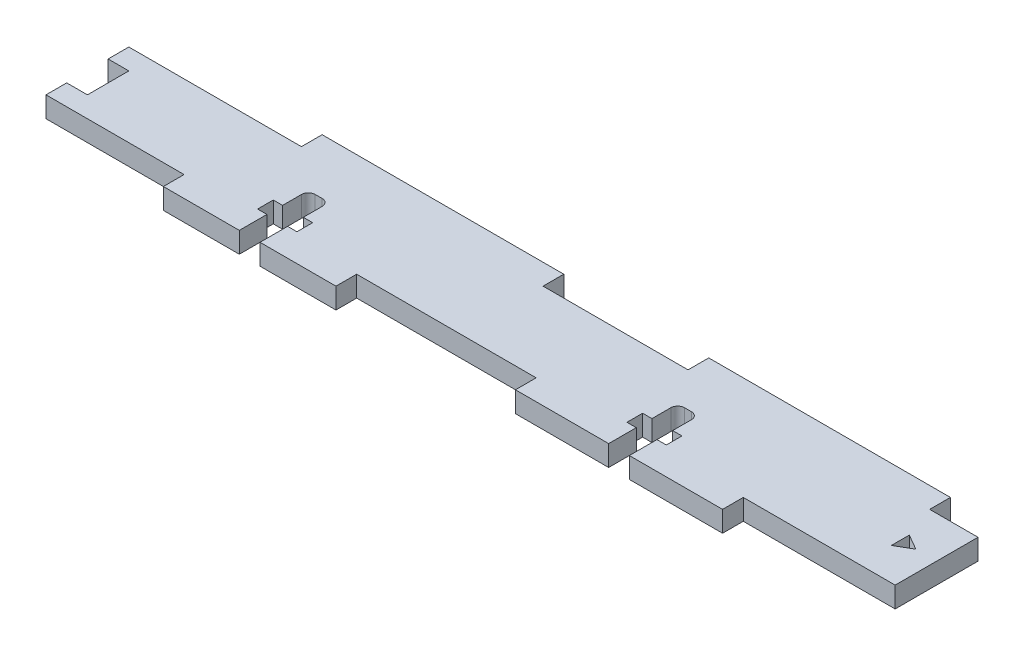
SolidWorks part; units mm, degrees
material "Acrylic (Medium-high impact)"
ref_plane "Plano frontal" through (0, 0, 0) normal (0, 0, 1) x (1, 0, 0)
ref_plane "Plano superior" through (0, 0, 0) normal (0, 1, 0) x (1, 0, 0)
ref_plane "Plano direito" through (0, 0, 0) normal (1, 0, 0) x (0, 0, -1)
sketch "Sketch1" plane through (0, 0, 0) normal (0, 1, 0) x (1, 0, 0)
  line L1 (-61.5, 6) -> (61.5, 6)
  line L2 (-61.5, 6) -> (-61.5, -6)
  line L3 (-61.5, -6) -> (61.5, -6)
  line L4 (61.5, 6) -> (61.5, -6)
  point P4 (0, 6)
  point P6 (-61.5, 0)
  dimension "D1" = 123
  dimension "D2" = 12
extrude "Boss-Extrude1" add sketch "Sketch1" along normal mid plane 3
sketch "Sketch2" plane through (0, 0, 0) normal (0, 1, 0) x (1, 0, 0)
  line L0 (-61.5, 6) -> (-61.5, -6) construction
  line L5 (-61.5, -6) -> (61.5, -6) construction
  line L6 (9.5, -6) -> (39.5, -6)
  line L7 (9.5, -6) -> (9.5, -9)
  line L8 (9.5, -9) -> (39.5, -9)
  line L9 (39.5, -6) -> (39.5, -9)
  dimension "D1" = 3
  dimension "D2" = 30
  dimension "D3" = 71
extrude "Boss-Extrude2" add sketch "Sketch2" along normal mid plane 3
sketch "Sketch12" plane through (0, 0, 0) normal (0, 1, 0) x (1, 0, 0)
  line L0 (-61.5, -6) -> (9.5, -6) construction
  line L1 (-41.5, -6) -> (-16.5, -6)
  line L2 (-41.5, -6) -> (-41.5, -9)
  line L3 (-41.5, -9) -> (-16.5, -9)
  line L4 (-16.5, -6) -> (-16.5, -9)
  line L5 (9.5, -9) -> (39.5, -9) construction
  line L6 (3.5, 6) -> (3.5, -6) construction
  line L7 (61.5, 6) -> (-61.5, 6) construction
  line L8 (-61.5, 6) -> (-61.5, -6) construction
  line L9 (3.5, 6) -> (-61.5, 6) construction
  line L10 (-29, 6) -> (-29, -6) construction
  point P18 (-29, -6)
  dimension "D2" = 25
  dimension "D3" = 20
  dimension "D4" = 20
extrude "Boss-Extrude3" add sketch "Sketch12" along normal mid plane 3
sketch "Sketch11" plane through (0, 0, 0) normal (0, 1, 0) x (1, 0, 0)
  line L0 (-41.5, -6) -> (-41.5, -9) construction
  line L5 (-30.5, -9) -> (-27.5, -9)
  line L6 (-30.5, -9) -> (-30.5, -5)
  line L20 (-3.5, -6) -> (-3.5, 6) construction
  line L34 (-41.5, -9) -> (-16.5, -9) construction
  line L44 (-29.5, 1) -> (-28.5, 1)
  line L45 (-27.5, -9) -> (-27.5, -5)
  line L46 (-30.5, -2.73) -> (-30.5, 0)
  line L47 (-31.85, -2.73) -> (-30.5, -2.73)
  line L48 (-31.85, -2.73) -> (-31.85, -5)
  line L49 (-31.85, -5) -> (-30.5, -5)
  line L50 (-26.15, -2.73) -> (-26.15, -5)
  line L51 (-27.5, -2.73) -> (-26.15, -2.73)
  line L52 (-27.5, -2.73) -> (-27.5, 0)
  line L53 (-27.5, -5) -> (-26.15, -5)
  line L54 (-16.5, -6) -> (9.5, -6) construction
  line L55 (61.5, 6) -> (-61.5, 6) construction
  line L70 (-16.5, -9) -> (-16.5, -6) construction
  line L71 (9.5, -9) -> (39.5, -9) construction
  line L72 (23, -9) -> (26, -9)
  line L73 (23, -9) -> (23, -5)
  line L74 (24, 1) -> (25, 1)
  line L75 (26, -9) -> (26, -5)
  line L76 (9.5, -6) -> (9.5, -9) construction
  line L77 (39.5, -9) -> (39.5, -6) construction
  line L78 (23, -2.73) -> (23, 0)
  line L79 (21.65, -2.73) -> (23, -2.73)
  line L80 (21.65, -2.73) -> (21.65, -5)
  line L81 (21.65, -5) -> (23, -5)
  line L82 (27.35, -2.73) -> (27.35, -5)
  line L83 (26, -2.73) -> (27.35, -2.73)
  line L84 (26, -2.73) -> (26, 0)
  line L85 (26, -5) -> (27.35, -5)
  arc A6 (-28.5, 1) -> (-27.5, 0) centre (-28.5, 0) cw
  arc A7 (-30.5, 0) -> (-29.5, 1) centre (-29.5, 0) cw
  arc A10 (25, 1) -> (26, 0) centre (25, 0) cw
  arc A11 (23, 0) -> (24, 1) centre (24, 0) cw
  point P16 (-27.5, 1)
  point P19 (-30.5, 1)
  dimension "D9" = 11
  dimension "D8" = 1
  dimension "D15" = 1
  dimension "D1" = 3
  dimension "D2" = 11
  dimension "D3" = 10
  dimension "D4" = 2.27
  dimension "D5" = 1.35
  dimension "D6" = 1.35
  dimension "D7" = 4
  dimension "D10" = 13.5
  dimension "D11" = 13.5
  dimension "D12" = 2.27
  dimension "D13" = 1.35
  dimension "D14" = 1.35
extrude "Cut-Extrude8" cut sketch "Sketch11" against normal through all both and the other way through all
sketch "Sketch13" plane through (0, 0, 0) normal (0, 1, 0) x (1, 0, 0)
  line L0 (61.5, 6) -> (-61.5, 6) construction
  line L1 (-36.5, 6) -> (-1.5, 6)
  line L2 (-36.5, 6) -> (-36.5, 9)
  line L3 (-36.5, 9) -> (-1.5, 9)
  line L4 (-1.5, 6) -> (-1.5, 9)
  line L5 (61.5, -6) -> (61.5, 6) construction
  line L10 (-61.5, 6) -> (-61.5, -6) construction
  line L12 (19.5, 9) -> (54.5, 9)
  line L13 (19.5, 9) -> (19.5, 6)
  line L14 (19.5, 6) -> (54.5, 6)
  line L15 (54.5, 9) -> (54.5, 6)
  dimension "D1" = 3
  dimension "D2" = 35
  dimension "D3" = 25
  dimension "D4" = 21
  dimension "D5" = 7
extrude "Boss-Extrude4" add sketch "Sketch13" along normal mid plane 3
sketch "Sketch15" plane through (0, 0, 0) normal (0, 1, 0) x (1, 0, 0)
  line L1 (56.25, -1.299) -> (58.5, 0)
  line L2 (58.5, 0) -> (56.25, 1.299)
  line L3 (56.25, 1.299) -> (56.25, -1.299)
  line L6 (61.5, -6) -> (61.5, 6) construction
  circle A0 centre (57, 0) radius 1.5 construction
  dimension "D1" = 3
  dimension "D2" = 3
extrude "Cut-Extrude10" cut sketch "Sketch15" against normal through all both and the other way through all
sketch "Sketch16" plane through (0, 0, 0) normal (0, 1, 0) x (1, 0, 0)
  line L0 (-61.5, 6) -> (-61.5, -6) construction
  line L1 (-61.5, 3) -> (-58.5, 3)
  line L2 (-61.5, 3) -> (-61.5, -3)
  line L3 (-61.5, -3) -> (-58.5, -3)
  line L4 (-58.5, 3) -> (-58.5, -3)
  line L6 (-61.5, -6) -> (-41.5, -6) construction
  point P6 (-58.5, 0)
  dimension "D1" = 3
  dimension "D2" = 6
  dimension "D3" = 3
extrude "Cut-Extrude11" cut sketch "Sketch16" against normal through all both and the other way through all
